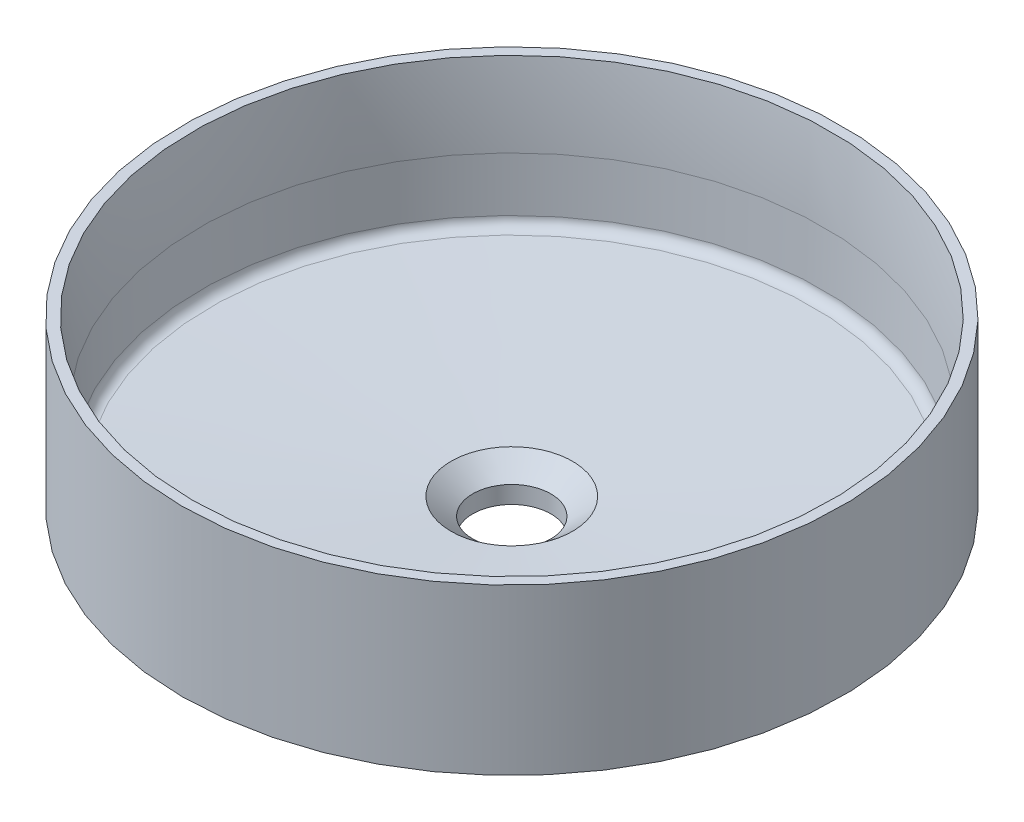
SolidWorks part; units mm, degrees
ref_plane "前视基准面" through (0, 0, 0) normal (0, 0, 1) x (1, 0, 0)
ref_plane "上视基准面" through (0, 0, 0) normal (0, 1, 0) x (1, 0, 0)
ref_plane "右视基准面" through (0, 0, 0) normal (1, 0, 0) x (0, 0, -1)
sketch "草图1" plane through (0, 0, 0) normal (0, 1, 0) x (1, 0, 0)
  circle A0 centre (0, 0) radius 190
  dimension "D1" = 380
extrude "凸台-拉伸1" add sketch "草图1" against normal blind 95
sketch "草图2" plane through (0, -95, 0) normal (0, -1, 0) x (1, 0, 0)
  circle A0 centre (0, 0) radius 167.5
  dimension "D1" = 335
extrude "凸台-拉伸2" add sketch "草图2" along normal blind 15
sketch "草图3" plane through (0, 0, 0) normal (0, 0, 1) x (1, 0, 0)
  line L0 (-184, 0) -> (-179, -82) construction
  line L1 (190, 0) -> (-190, 0) construction
  line L2 (-179, -82) -> (-35, -90)
  line L3 (-35, -90) -> (-22.5, -100)
  line L4 (-22.5, -100) -> (-22.5, -110)
  line L5 (-167.5, -110) -> (167.5, -110) construction
  line L6 (-22.5, -110) -> (0, -110)
  line L7 (0, -110) -> (0, 0)
  line L8 (0, 0) -> (-184, 0)
  line L9 (-180.2552, -46.0562) -> (-179, -82)
  line L10 (-157.5, -110) -> (-156.5, -93.2654)
  line L11 (-156.5, -93.2654) -> (-55, -98.9043)
  line L12 (-55, -98.9043) -> (-55, -110)
  line L13 (-55, -110) -> (-157.5, -110)
  line L14 (0, 0) -> (0, -240.0425) construction
  arc A0 (-184, 0) -> (-180.2552, -46.0562) centre (-679.9506, -63.5059) cw
  dimension "D9" = 500
  dimension "D1" = 179
  dimension "D2" = 6
  dimension "D3" = 82
  dimension "D4" = 90
  dimension "D5" = 22.5
  dimension "D6" = 35
  dimension "D7" = 10
  dimension "D8" = 88
  dimension "D10" = 10
  dimension "D11" = 10
  dimension "D12" = 55
  dimension "D13" = 1
ref_plane "基准面1" through (0, -97, 0) normal (0, -1, 0) x (-1, 0, 0)
sketch "草图4" plane through (0, -97, 0) normal (0, -1, 0) x (-1, 0, 0)
  circle A0 centre (0, 0) radius 167.5 construction
  circle A1 centre (0, 0) radius 167.5
loft "放样1" add profiles "草图4" section edge at (0, -95, 190) section "草图4"
fillet "圆角1" radius 5 1 edges at (0, -97, -167.5)
revolve "切除-旋转1" cut sketch "草图3" angle 360 about L14
fillet "圆角2" radius 6 1 edges at (0, -82, 179)
fillet "圆角3" radius 10 2 edges at (0, -98.9043, 55) (0, -93.2654, 156.5)
